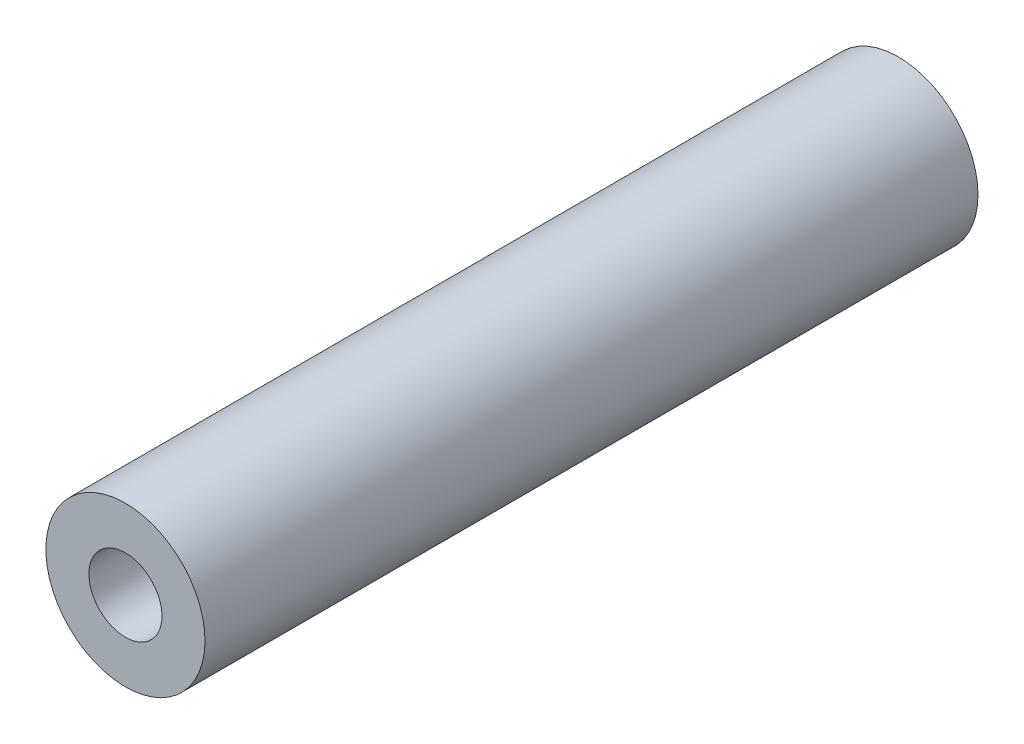
SolidWorks part; units mm, degrees
material "6061-T6 (SS)"
ref_plane "Front Plane" through (0, 0, 0) normal (0, 0, 1) x (1, 0, 0)
ref_plane "Top Plane" through (0, 0, 0) normal (0, 1, 0) x (1, 0, 0)
ref_plane "Right Plane" through (0, 0, 0) normal (1, 0, 0) x (0, 0, -1)
sketch "Sketch1" plane through (0, 0, 0) normal (0, 0, 1) x (1, 0, 0)
  circle A0 centre (0, 0) radius 2.5527
  circle A1 centre (0, 0) radius 5.5562
  dimension "D1" = 5.1054
  dimension "D2" = 11.1125
extrude "Boss-Extrude1" add sketch "Sketch1" along normal blind 53.975
